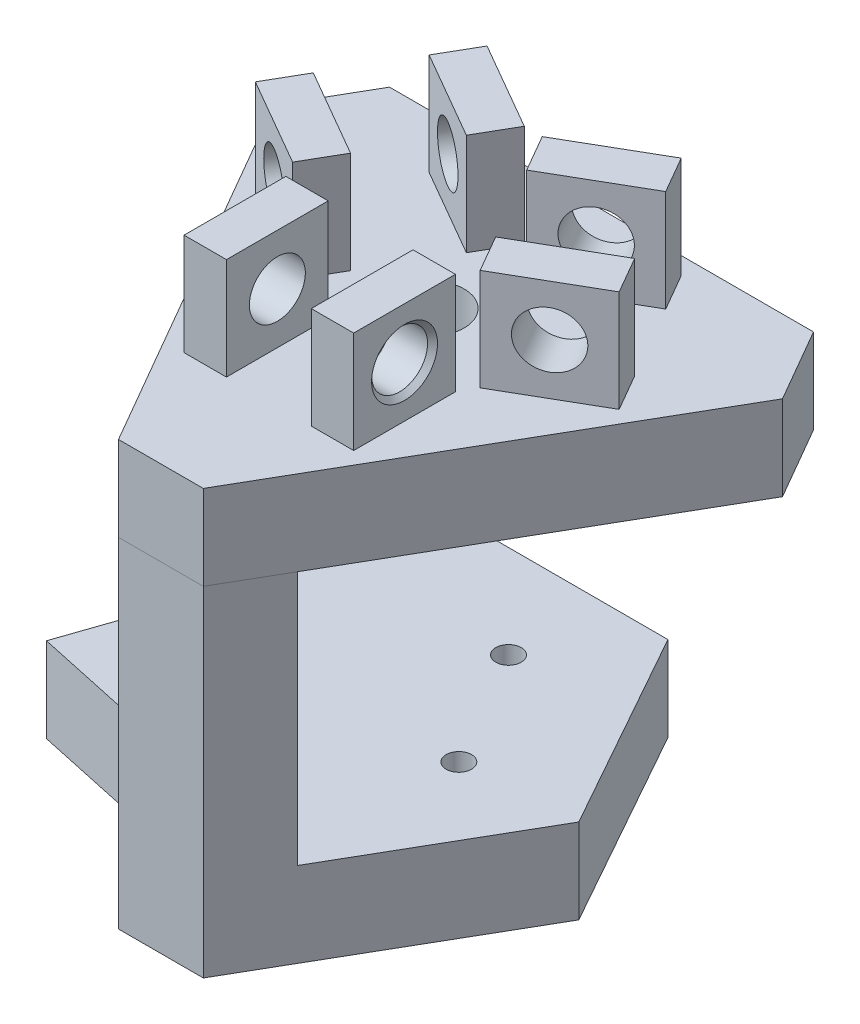
SolidWorks part; units mm, degrees
ref_plane "前视基准面" through (0, 0, 0) normal (0, 0, 1) x (1, 0, 0)
ref_plane "上视基准面" through (0, 0, 0) normal (0, 1, 0) x (1, 0, 0)
ref_plane "右视基准面" through (0, 0, 0) normal (1, 0, 0) x (0, 0, -1)
sketch "草图1" plane through (0, 0, 0) normal (0, 1, 0) x (1, 0, 0)
  line L0 (-32.8312, 24.6371) -> (17.1688, 24.6371)
  line L1 (17.1688, 24.6371) -> (22.1688, 15.9768)
  line L2 (22.1688, 15.9768) -> (-2.8312, -27.3245)
  line L3 (-2.8312, -27.3245) -> (-12.8312, -27.3245)
  line L4 (-12.8312, -27.3245) -> (-37.8312, 15.9768)
  line L5 (-32.8312, 24.6371) -> (-37.8312, 15.9768)
extrude "凸台-拉伸1" add sketch "草图1" along normal blind 10
sketch "草图2" plane through (0, 10, 0) normal (0, 1, 0) x (1, 0, 0)
  line L0 (-35.3312, 20.3069) -> (-7.8312, 4.4297) construction
  line L2 (-32.8312, 24.6371) -> (-37.8312, 15.9768) construction
  line L7 (-7.8312, 4.4297) -> (19.6688, 20.3069) construction
  line L8 (22.1688, 15.9768) -> (17.1688, 24.6371) construction
  line L14 (-7.8312, 4.4297) -> (-7.8312, -27.3245) construction
  line L15 (-12.8312, -27.3245) -> (-2.8312, -27.3245) construction
  line L20 (-8.8889, 16.5874) -> (-19.2812, 22.5874)
  line L21 (-8.8889, 16.5874) -> (-18.8889, -0.7331)
  line L24 (-19.2812, 22.5874) -> (-29.2812, 5.267)
  line L25 (-18.8889, -0.7331) -> (-29.2812, 5.267)
  line L30 (-8.8889, 16.5874) -> (-29.2812, 5.267) construction
  line L31 (-19.2812, 22.5874) -> (-18.8889, -0.7331) construction
  line L36 (13.6189, 5.267) -> (3.2266, -0.7331)
  line L37 (13.6189, 5.267) -> (3.6189, 22.5874)
  line L42 (3.2266, -0.7331) -> (-6.7734, 16.5874)
  line L43 (3.6189, 22.5874) -> (-6.7734, 16.5874)
  line L48 (13.6189, 5.267) -> (-6.7734, 16.5874) construction
  line L49 (3.2266, -0.7331) -> (3.6189, 22.5874) construction
  line L50 (2.1688, -14.5919) -> (2.1688, -2.5919)
  line L51 (2.1688, -14.5919) -> (-17.8312, -14.5919)
  line L52 (2.1688, -2.5919) -> (-17.8312, -2.5919)
  line L53 (-17.8312, -14.5919) -> (-17.8312, -2.5919)
  line L54 (2.1688, -14.5919) -> (-17.8312, -2.5919) construction
  line L55 (2.1688, -2.5919) -> (-17.8312, -14.5919) construction
  line L56 (-7.8312, -14.5919) -> (2.2937, -14.5919)
  line L57 (-17.8312, -14.5919) -> (-7.8312, -14.5919)
  line L58 (-17.8312, -2.5919) -> (-7.8312, -2.5919)
  line L59 (-7.8312, -2.5919) -> (2.1688, -2.5919)
  line L60 (-7.8312, -2.5919) -> (2.1688, -2.5919)
  line L61 (-2.8312, -2.5919) -> (-2.8312, -14.5919)
  line L62 (-17.8312, -14.5919) -> (-7.8312, -14.5919)
  line L63 (-12.8312, -14.5919) -> (-12.8312, -2.5919)
  line L64 (3.6189, 22.5874) -> (8.6189, 13.9272)
  line L65 (8.6189, 13.9272) -> (6.1189, 18.2573)
  line L66 (6.1189, 18.2573) -> (-4.2734, 12.2573)
  line L67 (3.2266, -0.7331) -> (-1.7734, 7.9272)
  line L68 (-1.7734, 7.9272) -> (0.7266, 3.5971)
  line L69 (0.7266, 3.5971) -> (11.1189, 9.5971)
  line L70 (-29.2812, 5.267) -> (-24.2812, 13.9272)
  line L71 (-24.2812, 13.9272) -> (-26.7812, 9.5971)
  line L72 (-26.7812, 9.5971) -> (-16.3889, 3.5971)
  line L73 (-24.2812, 13.9272) -> (-19.2812, 22.5874)
  line L74 (-21.7812, 18.2573) -> (-11.3889, 12.2573)
  circle A0 centre (-7.8312, 4.4297) radius 13 construction
  point P13 (-19.085, 10.9272)
  point P14 (3.4227, 10.9272)
  point P15 (-7.8312, -8.5919)
extrude "凸台-拉伸4" add sketch "草图2" along normal blind 12 contours L72 L70 L25 L21 | L24 L74 L21 L20 | L66 L64 L43 L42 | L69 L42 L36 L37 | L52 L61 L51 L50 | L62 L63 L58 L53
sketch "草图9" plane through (4.9603, 0, -8.5915) normal (0.5, 0, -0.866) x (-0.866, 0, -0.5)
  line L0 (21.9917, 10) -> (21.9917, 16)
  line L1 (15.9917, 10) -> (27.9917, 10) construction
hole_wizard "G1/16 螺纹孔1" positions "草图10" profile "草图11" tap size "G1/16" standard "GB"
sketch "草图10" plane through (4.9603, 0, -8.5915) normal (0.5, 0, -0.866) x (-0.866, 0, -0.5)
  point P0 (21.9917, 16)
sketch "草图11" plane through (-14.085, 16, -19.5874) normal (0, 1, 0) x (-0.866, 0, -0.5)
  line L0 (0, 0) -> (0, 51.9828)
  line L1 (0, 51.9828) -> (3.3, 50)
  line L2 (3.3, 50) -> (3.3, 0.5865)
  line L3 (3.3, 0.5865) -> (3.8865, 0)
  line L5 (3.8865, 0) -> (0, 0)
  line L6 (-3.3, 0.5865) -> (-3.8865, 0) construction
  line L10 (0, 51.9828) -> (-3.3, 50) construction
  line L11 (0, -6.35) -> (0, 107.95) construction
  dimension "螺纹孔钻头直径" = 6.6
  dimension "螺纹孔钻头深度" = 50
  dimension "近端锥形沉头孔直径" = 7.773
  dimension "近端锥形沉头孔角度" = 90
  dimension "导头角度" = 118
cosmetic thread "孔螺蚊线1" parameters "D1"=15.45, "D2"=7.723
sketch "草图12" plane through (-8.876, 0, -15.3735) normal (-0.5, 0, -0.866) x (-0.866, 0, 0.5)
  line L0 (-8.4278, 10) -> (-8.4278, 16)
  line L1 (-14.4278, 10) -> (-2.4278, 10) construction
hole_wizard "G1/16 螺纹孔2" positions "草图13" profile "草图14" tap size "G1/16" standard "GB"
sketch "草图13" plane through (-8.876, 0, -15.3735) normal (-0.5, 0, -0.866) x (-0.866, 0, 0.5)
  point P0 (-8.4278, 16)
sketch "草图14" plane through (-1.5773, 16, -19.5874) normal (0, 1, 0) x (-0.866, 0, 0.5)
  line L0 (0, 0) -> (0, 51.9828)
  line L1 (0, 51.9828) -> (3.3, 50)
  line L2 (3.3, 50) -> (3.3, 0.5865)
  line L3 (3.3, 0.5865) -> (3.8865, 0)
  line L5 (3.8865, 0) -> (0, 0)
  line L6 (-3.3, 0.5865) -> (-3.8865, 0) construction
  line L10 (0, 51.9828) -> (-3.3, 50) construction
  line L11 (0, -6.35) -> (0, 107.95) construction
  dimension "螺纹孔钻头直径" = 6.6
  dimension "螺纹孔钻头深度" = 50
  dimension "近端锥形沉头孔直径" = 7.773
  dimension "近端锥形沉头孔角度" = 90
  dimension "导头角度" = 118
cosmetic thread "孔螺蚊线2" parameters "D1"=15.45, "D2"=7.723
sketch "草图15" plane through (2.1688, 0, 0) normal (1, 0, 0) x (0, 0, -1)
  line L0 (-8.5919, 10) -> (-8.5919, 16)
  line L1 (-14.5919, 10) -> (-2.5919, 10) construction
hole_wizard "G1/16 螺纹孔3" positions "草图16" profile "草图17" tap size "G1/16" standard "GB"
sketch "草图16" plane through (2.1688, 0, 0) normal (1, 0, 0) x (0, 0, -1)
  point P0 (-8.5919, 16)
sketch "草图17" plane through (2.1688, 16, 8.5919) normal (0, 1, 0) x (0, 0, -1)
  line L0 (0, 0) -> (0, 51.9828)
  line L1 (0, 51.9828) -> (3.3, 50)
  line L2 (3.3, 50) -> (3.3, 0.5865)
  line L3 (3.3, 0.5865) -> (3.8865, 0)
  line L5 (3.8865, 0) -> (0, 0)
  line L6 (-3.3, 0.5865) -> (-3.8865, 0) construction
  line L10 (0, 51.9828) -> (-3.3, 50) construction
  line L11 (0, -6.35) -> (0, 107.95) construction
  dimension "螺纹孔钻头直径" = 6.6
  dimension "螺纹孔钻头深度" = 50
  dimension "近端锥形沉头孔直径" = 7.773
  dimension "近端锥形沉头孔角度" = 90
  dimension "导头角度" = 118
cosmetic thread "孔螺蚊线3" parameters "D1"=15.45, "D2"=7.723
sketch "草图18" plane through (0, 0, 0) normal (0, -1, 0) x (-1, 0, 0)
  line L0 (-17.1688, 24.6371) -> (-13.3775, 17.4073)
  line L1 (-13.3775, 17.4073) -> (-22.1688, 15.9768)
  line L2 (-13.3775, 0.7498) -> (0, 24.6371)
  line L3 (2.8312, -27.3245) -> (-22.1688, 15.9768) construction
  line L4 (-17.1688, 24.6371) -> (32.8312, 24.6371) construction
  line L5 (-13.3775, 0.7498) -> (-1.2378, -20.2769)
  line L6 (-1.2378, -20.2769) -> (36.5161, -12.1314)
  line L7 (-1.2378, -20.2769) -> (23.9153, 24.6371) construction
  line L8 (0, 24.6371) -> (23.9153, 24.6371)
  line L9 (23.9153, 24.6371) -> (36.5161, -12.1314)
  line M2 (32.8312, 24.6371) -> (-17.1688, 24.6371)
  line M4 (-22.1688, 15.9768) -> (2.8312, -27.3245)
  line M6 (12.8312, -27.3245) -> (37.8312, 15.9768)
extrude "凸台-拉伸5" add sketch "草图18" along normal blind 40 contours L9 L6 M6 | L7 L6 L9 M6 | L7 L2 M4 M2
sketch "草图19" plane through (-4.1251, 0, 19.1198) normal (-0.2109, 0, 0.9775) x (0.9775, 0, 0.2109)
  line L1 (-33.1362, 0) -> (16.8638, 0)
  line L2 (-33.1362, 0) -> (-33.1362, -30)
  line L3 (-33.1362, -30) -> (16.8638, -30)
  line L4 (16.8638, 0) -> (16.8638, -30)
extrude "切除-拉伸2" cut sketch "草图19" against normal blind 74
sketch "草图20" plane through (0, 0, 0) normal (0, -1, 0) x (1, 0, 0)
  line L0 (-12.8312, 27.3245) -> (-19.4809, 15.8068)
  line L1 (1.2378, 20.2769) -> (-36.5161, 12.1314) construction
  line L2 (-37.8312, -15.9768) -> (-12.8312, 27.3245) construction
  line L3 (-19.4809, 15.8068) -> (1.2378, 20.2769)
  line L4 (-2.8312, 27.3245) -> (22.1688, -15.9768) construction
  line L5 (1.2378, 20.2769) -> (-2.8312, 27.3245)
  line L6 (-2.8312, 27.3245) -> (-12.8312, 27.3245)
  line L7 (-37.8312, -15.9768) -> (-30.9611, -4.0776)
  line L8 (-23.9153, -24.6371) -> (-36.5161, 12.1314) construction
  line L9 (-30.9611, -4.0776) -> (-23.9153, -24.6371)
  line L10 (-23.9153, -24.6371) -> (-32.8312, -24.6371)
  line L11 (17.1688, -24.6371) -> (-32.8312, -24.6371) construction
  line L12 (-32.8312, -24.6371) -> (-37.8312, -15.9768) construction
  line L13 (-32.8312, -24.6371) -> (-37.8312, -15.9768)
extrude "凸台-拉伸6" add sketch "草图20" along normal blind 40
sketch "草图21" plane through (0, -40, 0) normal (0, -1, 0) x (-1, 0, 0)
  circle A0 centre (7.8312, 4.4298) radius 4.0139
sketch "草图23" plane through (0, -30, 0) normal (0, 1, 0) x (1, 0, 0)
  line L0 (-7.8312, 4.4298) -> (-7.8312, 24.6371) construction
  line L1 (-32.8312, 24.6371) -> (0, 24.6371) construction
  line L2 (-7.8312, 4.4298) -> (9.6688, -5.6738) construction
  line L3 (13.3775, 0.7498) -> (-2.8312, -27.3245) construction
  line L4 (-7.8312, 13.6674) -> (0.1688, -0.189)
  line L5 (-7.8312, 4.4298) -> (19.6688, 20.3069) construction
  line L6 (22.1688, 15.9768) -> (17.1688, 24.6371) construction
  circle A0 centre (0.1688, -0.189) radius 1.5
  circle A1 centre (-7.8312, 13.6674) radius 1.5
extrude "切除-拉伸3" cut sketch "草图23" against normal blind 6
sketch "草图24" plane through (0, 10, 0) normal (0, 1, 0) x (1, 0, 0)
  circle A0 centre (-7.8312, 4.4298) radius 4
extrude "切除-拉伸4" cut sketch "草图24" against normal blind 14
sketch "草图25" plane through (-35.2915, 0, -20.3756) normal (-0.866, 0, -0.5) x (-0.5, 0, 0.866)
  line L1 (-9.3787, 0) -> (48.0607, 0)
  line L2 (-9.3787, 0) -> (-9.3787, -0.001)
  line L3 (-9.3787, -0.001) -> (48.0607, -0.001)
  line L4 (48.0607, 0) -> (48.0607, -0.001)
  point P5 (0, 0)
split "分割1" trim tools "草图25" bodies to split 114 resulting bodies 125 126 127 128
